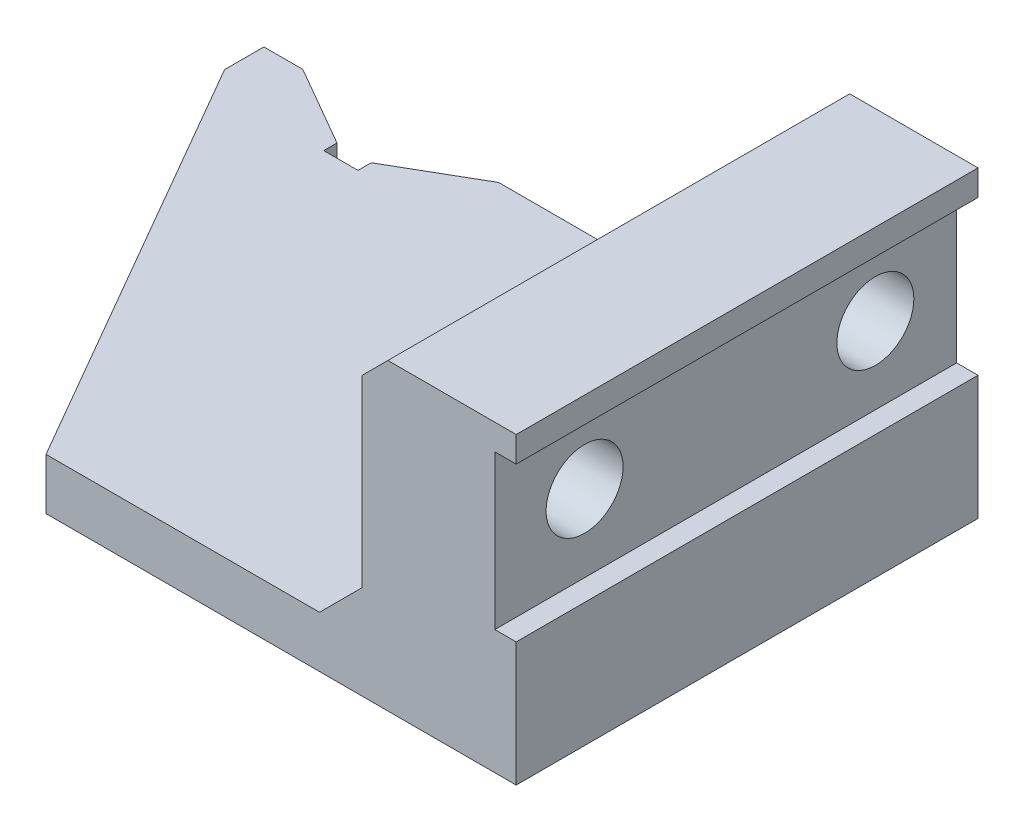
SolidWorks part; units mm, degrees
ref_plane "Ebene vorne" through (0, 0, 0) normal (0, 0, 1) x (1, 0, 0)
ref_plane "Ebene oben" through (0, 0, 0) normal (0, 1, 0) x (1, 0, 0)
ref_plane "Ebene rechts" through (0, 0, 0) normal (1, 0, 0) x (0, 0, -1)
sketch "Skizze1" plane through (0, 0, 0) normal (0, 0, 1) x (1, 0, 0)
  line L0 (-35.0769, 0) -> (97.1777, 0) construction
  line L1 (0, 6) -> (0, 0)
  line L2 (0, 0) -> (83.5, 0)
  line L3 (83.5, 0) -> (83.5, 14.5)
  line L4 (83.5, 14.5) -> (81, 14.5)
  line L5 (81, 14.5) -> (81, 32.5)
  line L6 (81, 32.5) -> (83.5, 32.5)
  line L7 (83.5, 32.5) -> (83.5, 35.5)
  line L8 (83.5, 35.5) -> (68.5, 35.5)
  line L9 (68.5, 35.5) -> (65.5, 32.5)
  line L10 (65.5, 32.5) -> (65.5, 11)
  line L11 (65.5, 11) -> (60.5, 6)
  line L12 (60.5, 6) -> (0, 6)
  point P5 (97.1777, 0)
  point P16 (83.5, 34)
  point P17 (0, 0)
  point P19 (0, 0)
  point P20 (71.2538, 35.5)
  dimension "D1" = 6
  dimension "D2" = 83.5
  dimension "D3" = 5
  dimension "D4" = 45
  dimension "D5" = 18
  dimension "D6" = 14.5
  dimension "D7" = 18
  dimension "D8" = 35.5
  dimension "D9" = 2.5
  dimension "D10" = 2.5
  dimension "D11" = 3
  dimension "D12" = 45
extrude "Aufsatz-Linear austragen1" add sketch "Skizze1" along normal blind 54
sketch "Skizze2" plane through (0, 6, 0) normal (0, 1, 0) x (1, 0, 0)
  line L0 (0, 0) -> (0, -4.6) construction
  line L1 (0, -54) -> (0, 0) construction
  line L2 (0, -4.6) -> (28.5211, -54)
  line L3 (60.5, -54) -> (0, -54) construction
  line L4 (28.5211, -54) -> (0, -54)
  line L5 (0, -54) -> (0, -4.6)
  line L6 (0, -54) -> (0, -4.6)
  line M4 (0, 0) -> (0, -54)
  line M5 (0, -54) -> (60.5, -54)
  dimension "D1" = 4.6
  dimension "D2" = 30
extrude "Schnitt-Linear austragen1" cut sketch "Skizze2" against normal through all contours L2 M4 M5
sketch "Skizze3" plane through (0, 6, 0) normal (0, 1, 0) x (1, 0, 0)
  line L0 (83.5, -54) -> (83.5, 0) construction
  line L1 (16, 7.82) -> (16, -12.6767) construction
  line L2 (0, 0) -> (-16.941, 0) construction
  line L3 (14, -7) -> (18, -7)
  line L4 (0, 0) -> (4.5554, 0)
  line L6 (60.5, 0) -> (0, 0) construction
  line L7 (4.5554, 0) -> (14, -5.4529)
  line L8 (14, -5.4529) -> (14, -7)
  line L9 (18, -7) -> (18, -5.4591)
  line L10 (18, -5.4591) -> (27.4554, 0)
  line L11 (4.5554, 0) -> (27.4554, 0)
  circle A0 centre (16, 7.82) radius 12.5 construction
  point P11 (4.5554, 0)
  point P18 (4.5554, 0)
  point P19 (3.0586, 0)
  line M10 (60.5, 0) -> (0, 0)
  dimension "D1" = 25
  dimension "D2" = 7.82
  dimension "D3" = 67.5
  dimension "D4" = 7
  dimension "D5" = 2
  dimension "D6" = 4
  dimension "D7" = 30
  dimension "D8" = 22.9
  dimension "D9" = 120
extrude "Schnitt-Linear austragen2" cut sketch "Skizze3" against normal through all contours L9 L10 L7 L8 L3 M10
sketch "Skizze4" plane through (81, 0, 0) normal (1, 0, 0) x (0, 0, -1)
  line L0 (-54.9516, 23.5) -> (1.6136, 23.5) construction
  circle A0 centre (-9.5, 23.5) radius 4.5
  circle A1 centre (-43.5, 23.5) radius 4.5
  dimension "D2" = 9
  dimension "D3" = 9
  dimension "D1" = 23.5
  dimension "D4" = 9.5
  dimension "D5" = 34
extrude "Schnitt-Linear austragen3" cut sketch "Skizze4" against normal up to next
sketch "Skizze5" plane through (65.5, 0, 0) normal (-1, 0, 0) x (0, 0, 1)
  circle A0 centre (43.5, 23.5) radius 7.5
  circle A1 centre (9.5, 23.5) radius 7.5
  dimension "D1" = 15
  dimension "D2" = 15
extrude "Schnitt-Linear austragen4" cut sketch "Skizze5" against normal blind 8
